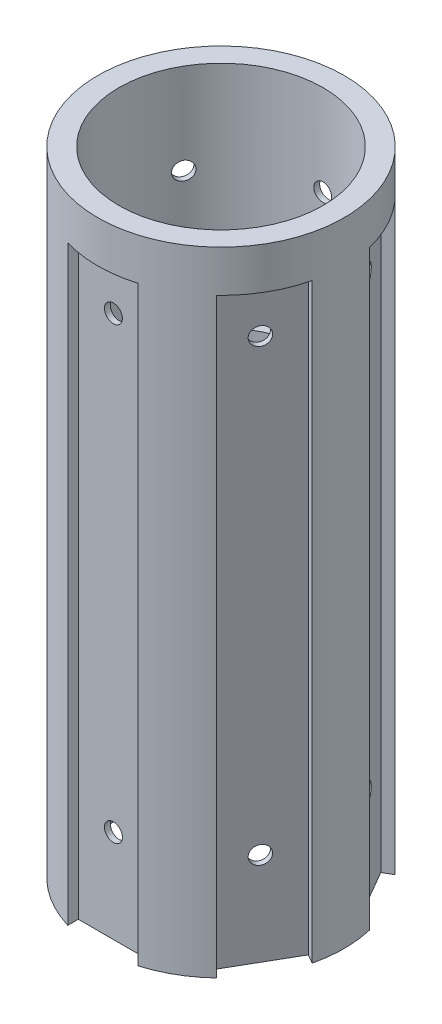
SolidWorks part; units mm, degrees
ref_plane "Front Plane" through (0, 0, 0) normal (0, 0, 1) x (1, 0, 0)
ref_plane "Top Plane" through (0, 0, 0) normal (0, 1, 0) x (1, 0, 0)
ref_plane "Right Plane" through (0, 0, 0) normal (1, 0, 0) x (0, 0, -1)
sketch "Sketch1" plane through (0, 0, 0) normal (0, 1, 0) x (1, 0, 0)
  circle A0 centre (0, 0) radius 23.36
  dimension "D1" = 46.72
extrude "Boss-Extrude1" add sketch "Sketch1" along normal blind 120
shell "Shell1" thickness 4
sketch "Sketch2" plane through (0, 0, 0) normal (0, -1, 0) x (1, 0, 0)
  line L0 (-4.8399, -13.5198) -> (-6.6452, -18.1838)
  line L3 (-4.4788, -12.5869) -> (-6.6452, -18.1838) construction
  line L4 (4.8399, -13.5198) -> (6.6452, -18.1838)
  line L5 (4.4788, -12.5869) -> (6.6452, -18.1838) construction
  line L6 (-14.1284, 2.5684) -> (-19.0702, 3.337)
  line L7 (-9.2885, 10.9514) -> (-12.4251, 14.8468)
  line L8 (9.2885, 10.9514) -> (12.4251, 14.8468)
  line L9 (14.1284, 2.5684) -> (19.0702, 3.337)
  circle A0 centre (0, 0) radius 19.36
  arc A1 (-19.3485, -0.6678) -> (-10.9935, -15.9359) centre (0, 0) ccw construction
  circle A2 centre (0, 0) radius 14.36
  circle A3 centre (0, 0) radius 17.275
  point P26 (0, 0)
  circle M5 centre (0, 0) radius 19.36
  dimension "D1" = 3
extrude "Boss-Extrude2" add sketch "Sketch2" against normal blind 28 from surface contours A3 L4 L9 M5 | A3 L6 L0 M5 | A3 L8 L7 M5
sketch "Sketch3" plane through (0, 0, -26.4) normal (0, 0, -1) x (-1, 0, 0)
  line L1 (-6.6533, 0) -> (6.6533, 0)
  line L2 (-6.6533, 0) -> (-6.6533, 112.0787)
  line L3 (-6.6533, 112.0787) -> (6.6533, 112.0787)
  line L4 (6.6533, 0) -> (6.6533, 112.0787)
  point P6 (0, 0)
  point P8 (0, 0)
extrude "Cut-Extrude2" cut sketch "Sketch3" against normal blind 3 from offset 3 offset against normal yes
pattern_circular "CirPattern1" count 6 over 360 about axis through (0, 0, 0) along (0, 1, 0) of "Cut-Extrude2"
sketch "Sketch4" plane through (0, 0, -20.4) normal (0, 0, -1) x (-1, 0, 0)
  line L0 (0, 0) -> (0, 109.795) construction
  line L1 (-6.6533, 0) -> (6.6533, 0) construction
  circle A0 centre (0, 102.8209) radius 1.7
  circle A1 centre (0, 17.6346) radius 1.7
  point P2 (0, 0)
  point P9 (0, 0)
  point P11 (0, 0)
  dimension "D1" = 3.4
extrude "Cut-Extrude3" cut sketch "Sketch4" against normal up to next
pattern_circular "CirPattern2" count 6 over 360 about axis through (0, 120, 0) along (0, -1, 0) of "Cut-Extrude3"
